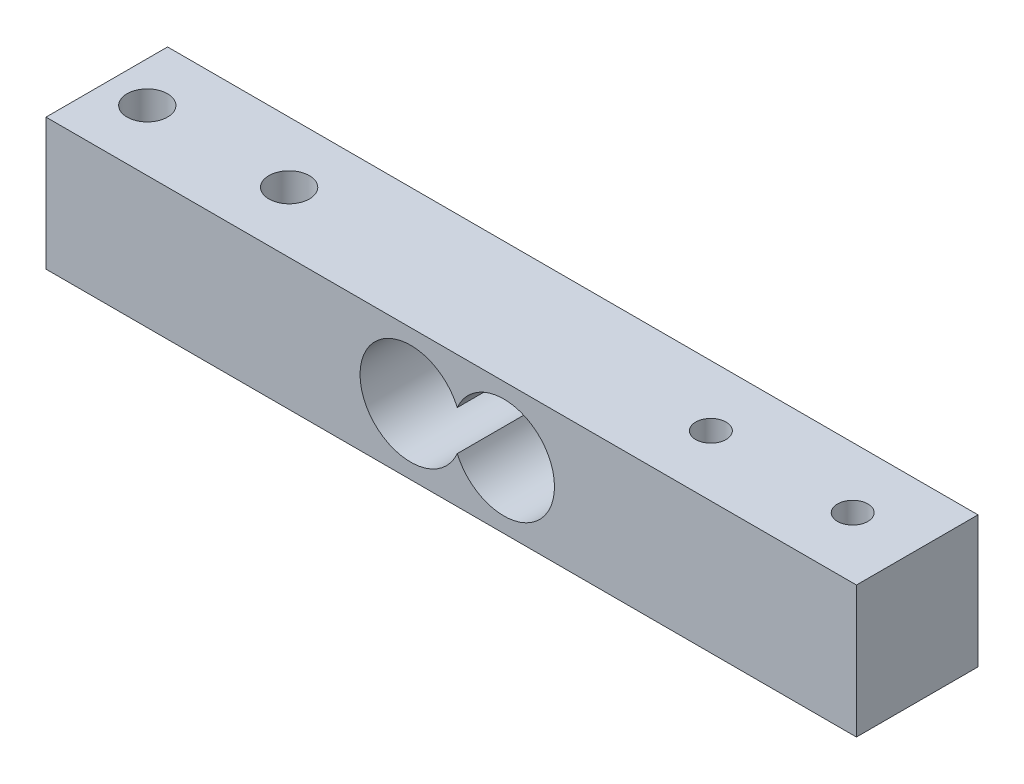
SolidWorks part; units mm, degrees
ref_plane "Front Plane" through (0, 0, 0) normal (0, 0, 1) x (1, 0, 0)
ref_plane "Top Plane" through (0, 0, 0) normal (0, 1, 0) x (1, 0, 0)
ref_plane "Right Plane" through (0, 0, 0) normal (1, 0, 0) x (0, 0, -1)
sketch "Sketch2" plane through (0, 0, 0) normal (0, 1, 0) x (1, 0, 0)
  line L1 (-40, -6) -> (40, -6)
  line L2 (-40, -6) -> (-40, 6)
  line L3 (-40, 6) -> (40, 6)
  line L4 (40, -6) -> (40, 6)
  line L5 (-40, -6) -> (40, 6) construction
  line L6 (-40, 6) -> (40, -6) construction
  point P0 (0, 0)
  dimension "D1" = 80
  dimension "D2" = 12
sketch "Sketch3" plane through (0, 0, 0) normal (0, 1, 0) x (1, 0, 0)
  line L0 (-40, 0) -> (-36, 0) construction
  line L2 (40, 0) -> (33.6316, 0) construction
  line L3 (-40, -6) -> (-40, 6) construction
  line L4 (-36, 0) -> (-22, 0) construction
  line L5 (40, -6) -> (40, 6) construction
  line L6 (33.6316, 0) -> (19.6316, 0) construction
  circle A0 centre (-36, 0) radius 2
  circle A1 centre (-22, 0) radius 2
  circle A2 centre (33.6316, 0) radius 1.5
  circle A3 centre (19.6316, 0) radius 1.5
extrude "Boss-Extrude1" add sketch "Sketch2" along normal blind 13
extrude "Cut-Extrude1" cut sketch "Sketch3" along normal blind 13
sketch "Sketch4" plane through (0, 0, 0) normal (0, 0, 1) x (1, 0, 0)
  line L0 (-40, 6.5) -> (-9, 6.5) construction
  line L1 (-40, 13) -> (40, 13)
  line L2 (-40, 13) -> (-40, 0)
  line L3 (-40, 0) -> (40, 0)
  line L4 (40, 13) -> (40, 0)
  line L5 (40, 6.5) -> (10.1935, 6.5) construction
  line L6 (-9, 6.5) -> (-4, 6.5) construction
  line L7 (10.1935, 6.5) -> (5.1935, 6.5) construction
  circle A0 centre (-4, 6.5) radius 5
  circle A1 centre (5.1935, 6.5) radius 5
extrude "Cut-Extrude2" cut sketch "Sketch4" against normal blind 6.5 and the other way blind 6.5 contours A1 | A0
sketch "Sketch5" plane through (40, 0, 0) normal (1, 0, 0) x (0, 0, -1)
  line L0 (0, 6.3944) -> (0, 2.1975) construction
  line L1 (0, 2.1975) -> (1.9589, 3.965)
  line L2 (1.9589, 3.965) -> (-1.9797, 3.965)
  line L3 (-1.9797, 3.965) -> (0, 2.1975)
  line L4 (-1.9797, 3.965) -> (-0.0104, 3.965)
  line L5 (-0.0104, 3.965) -> (2.0281, 3.965)
  line L6 (2.0281, 3.965) -> (1.0089, 3.965)
  line L7 (1.0089, 3.965) -> (1.0089, 6.3944)
  line L8 (1.0089, 6.3944) -> (-0.9951, 6.3944)
  line L9 (-0.9951, 6.3944) -> (-0.9951, 3.965)
  line L10 (-0.9951, 3.965) -> (-0.0104, 3.965)
  line L11 (-0.0104, 3.965) -> (-0.0572, 3.9899)
